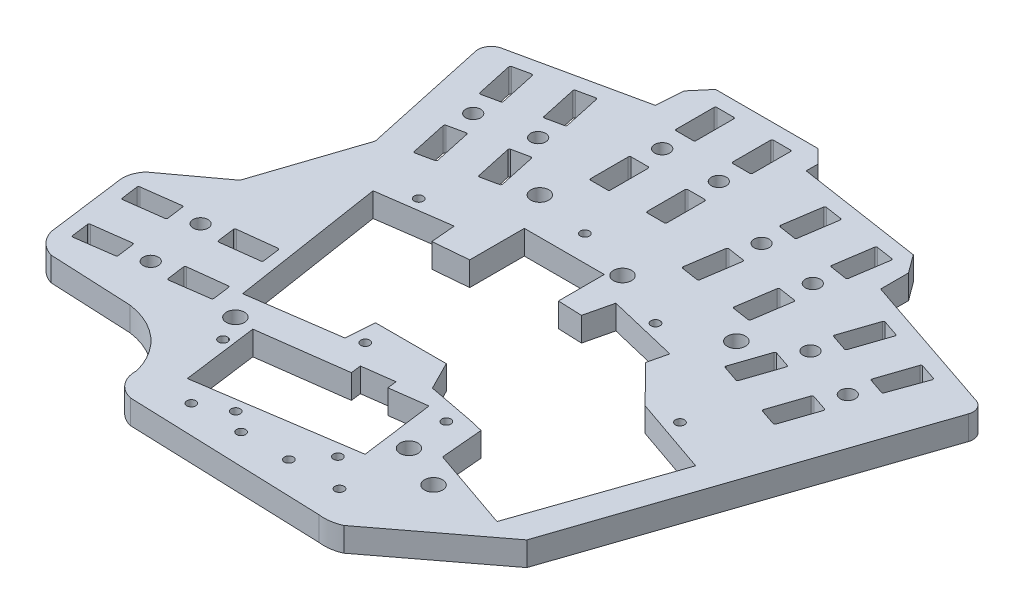
SolidWorks part; units mm, degrees
ref_plane "Front Plane" through (0, 0, 0) normal (0, 0, 1) x (1, 0, 0)
ref_plane "Top Plane" through (0, 0, 0) normal (0, 1, 0) x (1, 0, 0)
ref_plane "Right Plane" through (0, 0, 0) normal (1, 0, 0) x (0, 0, -1)
sketch "Sketch1" plane through (0, 0, 0) normal (0, 1, 0) x (1, 0, 0)
  line L0 (414.8299, -62.9754) -> (414.8299, 577.0246) construction
  line L1 (0, -2.5947) -> (-1.673, 9.9781)
  line L128 (-0.4306, 75.7337) -> (-0.1016, 80.2321)
  line L129 (44.8017, 72.6509) -> (44.8017, 68.0109)
  line L130 (-18.2349, 69.3257) -> (-15.0094, 70.0232)
  line L131 (-13.7962, 48.8002) -> (-15.2229, 55.3977)
  line L132 (17.4784, 66.3016) -> (14.1784, 66.3016)
  line L136 (-8.0429, 64.6237) -> (-4.8175, 65.3212)
  line L137 (37.2899, 67.114) -> (40.5526, 66.6193)
  line L138 (47.537, 57.3204) -> (49.7003, 63.7144)
  line L139 (50.663, 56.2628) -> (47.537, 57.3204)
  line L140 (-15.9879, 9.9957) -> (-16.4404, 13.4126)
  line L141 (-30.1274, 8.2215) -> (-30.567, 11.5414)
  line L142 (12.5856, 13.6137) -> (17.8315, 14.3117)
  line L145 (-0.1016, 80.2321) -> (2.2923, 83.0516)
  line L146 (-13.5827, 63.4257) -> (-16.8082, 62.7282)
  line L147 (-6.2442, 71.9187) -> (-9.4696, 71.2212)
  line L148 (49.7003, 63.7144) -> (52.8262, 62.6568)
  line L149 (-17.2671, 19.6546) -> (-10.5698, 20.4923)
  line L150 (24.079, 13.5635) -> (25.7132, 1.2828)
  line L152 (-9.4696, 71.2212) -> (-8.0429, 64.6237)
  line L153 (14.1784, 80.5516) -> (14.1784, 73.8016)
  line L154 (28.2605, 75.3105) -> (31.5232, 74.8157)
  line L155 (-10.5698, 20.4923) -> (-11.003, 23.7637)
  line L158 (-29.1205, 3.861) -> (-15.3607, 3.2228)
  line L159 (4.748, 80.5516) -> (8.048, 80.5516)
  line L160 (25.1119, 54.5479) -> (26.1239, 61.2216)
  line L161 (-17.7067, 22.9746) -> (-17.2671, 19.6546)
  line L162 (17.8315, 14.3117) -> (18.038, 12.7597)
  line L164 (-4.9467, 50.7139) -> (-1.7212, 51.4114)
  line L165 (31.5232, 74.8157) -> (30.5111, 68.142)
  line L166 (36.1654, 59.6988) -> (35.1534, 53.0251)
  line L167 (-24.7018, 18.6674) -> (-25.1351, 21.9389)
  line L169 (42.5794, 75.6677) -> (44.8017, 72.6509)
  line L170 (8.048, 66.3016) -> (8.048, 59.5516)
  line L171 (29.3866, 60.7268) -> (28.3746, 54.0531)
  line L172 (-23.8755, 12.4276) -> (-23.4422, 9.1562)
  line L173 (-9.7367, 14.2018) -> (-9.3035, 10.9303)
  line L175 (44.8017, 68.0109) -> (66.3992, 60.704)
  line L176 (-10.5708, 49.4977) -> (-13.7962, 48.8002)
  line L177 (4.748, 73.8016) -> (4.748, 80.5516)
  line L178 (38.4161, 52.5303) -> (39.4281, 59.204)
  line L179 (42.9702, 43.822) -> (45.1334, 50.216)
  line L180 (-31.8266, 21.0527) -> (-31.3934, 17.7812)
  line L181 (12.8129, 11.9057) -> (12.5856, 13.6137)
  line L182 (25.7132, 1.2828) -> (0, -2.5947)
  line L183 (-21.396, 71.1999) -> (-0.4306, 75.7337)
  line L184 (-16.8082, 62.7282) -> (-18.2349, 69.3257)
  line L185 (17.4784, 80.5516) -> (14.1784, 80.5516)
  line L186 (17.4784, 59.5516) -> (17.4784, 66.3016)
  line L187 (56.9812, 54.1252) -> (59.9745, 53.1125)
  line L188 (48.2594, 49.1584) -> (46.0962, 42.7644)
  line L189 (57.6372, 45.9857) -> (54.5113, 47.0433)
  line L190 (-16.4404, 13.4126) -> (-9.7367, 14.2018)
  line L192 (27.2484, 68.6368) -> (28.2605, 75.3105)
  line L193 (52.8262, 62.6568) -> (50.663, 56.2628)
  line L194 (59.1439, 60.5178) -> (56.9812, 54.1252)
  line L195 (52.3481, 40.6493) -> (55.474, 39.5917)
  line L196 (-23.4422, 9.1562) -> (-30.1274, 8.2215)
  line L197 (-1.673, 9.9781) -> (12.8129, 11.9057)
  line L200 (-15.0094, 70.0232) -> (-13.5827, 63.4257)
  line L201 (8.048, 73.8016) -> (4.748, 73.8016)
  line L202 (14.1784, 59.5516) -> (17.4784, 59.5516)
  line L203 (39.4281, 59.204) -> (36.1654, 59.6988)
  line L204 (46.0962, 42.7644) -> (42.9702, 43.822)
  line L208 (2.2923, 83.0516) -> (19.2923, 83.0516)
  line L209 (21.5696, 78.8537) -> (42.5794, 75.6677)
  line L210 (-24.2083, 30.3699) -> (-33.1809, 23.7603)
  line L211 (-15.2229, 55.3977) -> (-11.9975, 56.0952)
  line L212 (-6.3734, 57.3114) -> (-4.9467, 50.7139)
  line L213 (14.1784, 66.3016) -> (14.1784, 59.5516)
  line L214 (54.5113, 47.0433) -> (52.3481, 40.6493)
  line L217 (-18.5836, 47.2829) -> (-23.2066, 68.6607)
  line L218 (19.2923, 83.0516) -> (21.5696, 80.8227)
  line L219 (-34.2129, 20.029) -> (-32.5222, 7.2627)
  line L220 (-4.8175, 65.3212) -> (-6.2442, 71.9187)
  line L221 (-3.1479, 58.0089) -> (-6.3734, 57.3114)
  line L222 (4.748, 66.3016) -> (8.048, 66.3016)
  line L223 (40.5526, 66.6193) -> (41.5647, 73.293)
  line L224 (41.5647, 73.293) -> (38.302, 73.7877)
  line L226 (-24.2083, 30.3699) -> (-18.5836, 47.2829)
  line L227 (14.1784, 73.8016) -> (17.4784, 73.8016)
  line L228 (30.5111, 68.142) -> (27.2484, 68.6368)
  line L229 (38.302, 73.7877) -> (37.2899, 67.114)
  line L230 (-25.1351, 21.9389) -> (-31.8266, 21.0527)
  line L231 (-11.003, 23.7637) -> (-17.7067, 22.9746)
  line L233 (21.5696, 80.8227) -> (21.5696, 78.8537)
  line L234 (-1.9091, -10.1276) -> (30.562, -11.2693)
  line L235 (17.4784, 73.8016) -> (17.4784, 80.5516)
  line L236 (4.748, 59.5516) -> (4.748, 66.3016)
  line L237 (26.1239, 61.2216) -> (29.3866, 60.7268)
  line L239 (-9.3035, 10.9303) -> (-15.9879, 9.9957)
  line L241 (-11.9975, 56.0952) -> (-10.5708, 49.4977)
  line L242 (35.1534, 53.0251) -> (38.4161, 52.5303)
  line L243 (62.2699, 59.4603) -> (59.1439, 60.5178)
  line L244 (-31.3934, 17.7812) -> (-24.7018, 18.6674)
  line L245 (-30.567, 11.5414) -> (-23.8755, 12.4276)
  line L246 (18.038, 12.7597) -> (24.079, 13.5635)
  line L247 (-1.7212, 51.4114) -> (-3.1479, 58.0089)
  line L248 (8.048, 80.5516) -> (8.048, 73.8016)
  line L249 (8.048, 59.5516) -> (4.748, 59.5516)
  line L250 (28.3746, 54.0531) -> (25.1119, 54.5479)
  line L251 (45.1334, 50.216) -> (48.2594, 49.1584)
  line L252 (55.474, 39.5917) -> (57.6372, 45.9857)
  line L254 (-13.6102, 55.7464) -> (-15.1954, 63.077) construction
  line L256 (59.9745, 53.1125) -> (62.2699, 59.4603)
  line L257 (-4.7607, 57.6601) -> (-6.4302, 64.9725) construction
  line L258 (6.398, 66.3016) -> (6.398, 73.8016) construction
  line L259 (15.8284, 66.3016) -> (15.8284, 73.8016) construction
  line L260 (46.6964, 49.6872) -> (47.069, 50.7886) construction
  line L261 (56.0742, 46.5145) -> (58.4778, 53.6189) construction
  line L262 (-24.9184, 20.3032) -> (-17.4869, 21.3146) construction
  line L263 (-16.2142, 11.7042) -> (-23.6588, 10.7919) construction
  line L264 (27.7553, 60.9742) -> (28.8798, 68.3894) construction
  line L265 (37.7968, 59.4514) -> (38.9213, 66.8666) construction
  line L272 (66.3992, 60.704) -> (68.8544, 59.8733)
  line L273 (70.108, 57.3378) -> (51.5211, 2.3994)
  line L274 (51.5211, 2.3994) -> (34.2012, -10.7501)
  line L299 (47.4976, 52.0553) -> (49.1, 56.7916) construction
  line L302 (19.7057, 47.104) -> (19.7057, 42.0865)
  line L309 (7.2943, 16.3661) -> (7.6276, 21.104)
  line L310 (7.6276, 21.104) -> (19.4078, 21.104)
  line L317 (-10.9036, 40.0286) -> (4.9406, 42.2472) construction
  line L319 (0.2418, 41.5893) -> (0.598, 37.5071)
  line L320 (0.598, 37.5071) -> (6.398, 38.0133)
  line L321 (6.398, 38.0133) -> (6.398, 47.104)
  line L322 (6.398, 47.104) -> (19.7057, 47.104)
  line L323 (19.7057, 42.0865) -> (19.7057, 39.4743)
  line L324 (24.8019, 43.9355) -> (23.6987, 39.3179)
  line L325 (23.6987, 39.3179) -> (19.7057, 39.4743)
  line L326 (24.8019, 43.9355) -> (36.6086, 41.1145)
  line L327 (25.1826, 43.2788) -> (36.6086, 41.1145) construction
  line L328 (36.6086, 41.1145) -> (35.941, 37.5897) construction
  line L329 (36.6086, 41.1145) -> (35.8276, 37.8454)
  line L330 (35.8276, 37.8454) -> (42.0285, 31.5818)
  line L332 (32.5456, 7.3504) -> (46.3891, 2.5621)
  line L333 (46.3891, 2.5621) -> (54.8882, 27.1338)
  line L335 (42.0285, 31.5818) -> (54.8882, 27.1338)
  line L337 (19.4078, 21.104) -> (21.7804, 16.4205)
  line L338 (21.7804, 16.4205) -> (29.6863, 14.9001)
  line L339 (29.6863, 14.9001) -> (31.9336, 14.3632)
  line L340 (-11.6079, 39.93) -> (-7.6294, 14.2361)
  line L341 (-7.6294, 14.2361) -> (7.2943, 16.3661)
  line L342 (-11.6079, 39.93) -> (0.2418, 41.5893)
  line L345 (31.9336, 14.3632) -> (32.5456, 7.3504)
  arc A39 (-33.1809, 23.7603) -> (-34.2129, 20.029) centre (-30.0537, 20.8871) ccw
  circle A40 centre (-5.5285, 61.3308) radius 1.25
  circle A41 centre (15.8284, 70.0516) radius 1.25
  circle A43 centre (-14.4198, 59.408) radius 1.25
  circle A44 centre (12.1847, 51.3928) radius 0.75
  arc A45 (-15.3607, 3.2228) -> (-5.337, -5.6661) centre (-16.9425, -8.657) cw
  circle A46 centre (47.8982, 53.2394) radius 1.25
  circle A48 centre (-4.8264, 10.2313) radius 1.5
  circle A49 centre (-2.6471, 5.9989) radius 0.75
  circle A50 centre (3.9045, -5.8292) radius 0.75
  circle A51 centre (23.7898, -1.3252) radius 0.75
  arc A53 (34.2012, -10.7501) -> (30.562, -11.2693) centre (31.4838, -4.7168) cw
  circle A54 centre (28.3175, 64.6818) radius 1.25
  circle A55 centre (40.317, 48.4759) radius 1.5
  circle A57 centre (20.131, -5.8292) radius 0.75
  circle A59 centre (-21.2027, 20.8089) radius 1.25
  arc A61 (-32.5222, 7.2627) -> (-29.1205, 3.861) centre (-27.7256, 8.6576) ccw
  circle A62 centre (6.398, 70.0516) radius 1.25
  circle A63 centre (-19.9365, 11.248) radius 1.25
  arc A64 (-5.337, -5.6661) -> (-1.9091, -10.1276) centre (-1.006, -5.886) ccw
  circle A65 centre (38.359, 63.159) radius 1.25
  circle A66 centre (8.761, -3.2983) radius 0.75
  circle A67 centre (28.5591, -5.8292) radius 0.75
  circle A69 centre (2.8796, 53.2042) radius 1.5
  circle A70 centre (21.3669, 48.4759) radius 1.5
  circle A71 centre (28.4975, 5.8033) radius 1.5
  arc A72 (-23.2066, 68.6607) -> (-21.396, 71.1999) centre (-21.0316, 69.025) cw
  circle A73 centre (57.276, 50.0667) radius 1.25
  circle A74 centre (12.1847, -5.8292) radius 0.75
  arc A77 (70.108, 57.3378) -> (68.8544, 59.8733) centre (68.2134, 57.9788) ccw
  circle A79 centre (30.9955, 44.343) radius 0.75
  circle A80 centre (47.3149, 32.0935) radius 0.75
  circle A81 centre (-6.6778, 42.6019) radius 0.75
  circle A83 centre (9.6505, 17.369) radius 0.7627
  circle A84 centre (35.8276, 2.5621) radius 1.5
  circle A85 centre (27.7553, 12.7597) radius 0.75
  point P28 (-5.7897, 41.1181)
  point P29 (12.1847, 50.6428)
  point P30 (31.1361, 45.7394)
  point P31 (47.2602, 34.058)
  point P32 (-3.3264, 10.2313)
  point P38 (14.3264, -10.6984)
  dimension "D18" = 2.5
  dimension "D19" = 2.5
  dimension "D28" = 2.5
  dimension "D29" = 2.5
  dimension "D41" = 2.5
  dimension "D42" = 2.5
  dimension "D53" = 2.5
  dimension "D54" = 2.5
  dimension "D64" = 2.5
  dimension "D65" = 2.5
  dimension "D35" = 3
  dimension "D62" = 3
  dimension "D63" = 3
  dimension "D67" = 3
  dimension "D75" = 3
  dimension "D76" = 1.5254
  dimension "D77" = 1.5
  dimension "D78" = 1.5
  dimension "D79" = 1.5
  dimension "D80" = 1.5
  dimension "D81" = 1.5
  dimension "D82" = 1.5
  dimension "D83" = 1.5
  dimension "D84" = 1.5
  dimension "D85" = 1.5
  dimension "D86" = 1.5
  dimension "D87" = 26
  dimension "D88" = 26
  dimension "D89" = 1.5
  dimension "D94" = 2
  dimension "D34" = 1.5
  dimension "D92" = 3
  dimension "D100" = 26
  dimension "D1" = 2.5
  dimension "D2" = 17
  dimension "D4" = 22.8
  dimension "D5" = 21.25
  dimension "D6" = 2.5
  dimension "D7" = 2.5
  dimension "D8" = 2.5
  dimension "D9" = 2.5
  dimension "D10" = 2.5
  dimension "D11" = 2.5
  dimension "D12" = 21.45
  dimension "D13" = 3.3
  dimension "D14" = 3.3
  dimension "D15" = 2.5
  dimension "D16" = 3.3
  dimension "D17" = 3.3
  dimension "D20" = 3.3
  dimension "D21" = 3.3
  dimension "D22" = 3.3
  dimension "D23" = 6.75
  dimension "D24" = 3.3
  dimension "D25" = 6.75
  dimension "D26" = 6.75
  dimension "D27" = 6.75
  dimension "D30" = 6.75
  dimension "D31" = 6.75
  dimension "D32" = 6.75
  dimension "D33" = 6.75
  dimension "D36" = 7.5
  dimension "D37" = 3.3
  dimension "D38" = 3.3
  dimension "D39" = 6.75
  dimension "D40" = 6.75
  dimension "D43" = 7.5
  dimension "D44" = 6.75
  dimension "D45" = 6.75
  dimension "D46" = 6.75
  dimension "D47" = 6.75
  dimension "D48" = 6.75
  dimension "D49" = 3.3
  dimension "D50" = 3.3
  dimension "D51" = 3.3
  dimension "D52" = 3.3
  dimension "D55" = 7.5
  dimension "D56" = 6.75
  dimension "D57" = 6.75
  dimension "D58" = 6.75
  dimension "D59" = 6.75
  dimension "D60" = 3.75
  dimension "D61" = 3.75
  dimension "D66" = 3.75
  dimension "D68" = 3.75
  dimension "D69" = 3.75
  dimension "D70" = 3.75
  dimension "D71" = 3.75
  dimension "D72" = 3.75
  dimension "D73" = 3.75
  dimension "D74" = 7.5
  dimension "D90" = 4.5
  dimension "D91" = 5.8
  dimension "D93" = 93.75
  dimension "D95" = 26
  dimension "D96" = 6.67
  dimension "D97" = 3.3
  dimension "D98" = 3.3
  dimension "D99" = 3.3
extrude "Boss-Extrude1" add sketch "Sketch1" along normal blind 4
fillet "Fillet2" radius 0.25 80 edges at (-23.4422, 2, -9.1562) (-9.3035, 2, -10.9303) (-10.5698, 2, -20.4923) (-24.7018, 2, -18.6674) (-9.7367, 2, -14.2018) (-23.8755, 2, -12.4276) (-11.003, 2, -23.7637) (-25.1351, 2, -21.9389) (-17.7067, 2, -22.9746) (-16.4404, 2, -13.4126) (-30.567, 2, -11.5414) (-31.8266, 2, -21.0527) (-17.2671, 2, -19.6546) (-15.9879, 2, -9.9957) (-30.1274, 2, -8.2215) (-31.3934, 2, -17.7812) (55.474, 2, -39.5917) (52.3481, 2, -40.6493) (57.6372, 2, -45.9857) (54.5113, 2, -47.0433) (46.0962, 2, -42.7644) (42.9702, 2, -43.822) (48.2594, 2, -49.1584) (45.1334, 2, -50.216) (62.2699, 2, -59.4603) (59.9745, 2, -53.1125) (59.1439, 2, -60.5178) (56.9812, 2, -54.1252) (52.8262, 2, -62.6568) (50.663, 2, -56.2628) (47.537, 2, -57.3204) (49.7003, 2, -63.7144) (38.302, 2, -73.7877) (36.1654, 2, -59.6988) (40.5526, 2, -66.6193) (38.4161, 2, -52.5303) (28.3746, 2, -54.0531) (26.1239, 2, -61.2216) (29.3866, 2, -60.7268) (39.4281, 2, -59.204) (41.5647, 2, -73.293) (37.2899, 2, -67.114) (35.1534, 2, -53.0251) (25.1119, 2, -54.5479) (27.2484, 2, -68.6368) (31.5232, 2, -74.8157) (30.5111, 2, -68.142) (28.2605, 2, -75.3105) (17.4784, 2, -59.5516) (14.1784, 2, -59.5516) (17.4784, 2, -66.3016) (14.1784, 2, -66.3016) (8.048, 2, -59.5516) (4.748, 2, -59.5516) (8.048, 2, -66.3016) (4.748, 2, -66.3016) (17.4784, 2, -73.8016) (14.1784, 2, -73.8016) (8.048, 2, -73.8016) (4.748, 2, -73.8016) (14.1784, 2, -80.5516) (17.4784, 2, -80.5516) (8.048, 2, -80.5516) (4.748, 2, -80.5516) (-1.7212, 2, -51.4114) (-4.9467, 2, -50.7139) (-3.1479, 2, -58.0089) (-6.3734, 2, -57.3114) (-10.5708, 2, -49.4977) (-13.7962, 2, -48.8002) (-11.9975, 2, -56.0952) (-15.2229, 2, -55.3977) (-4.8175, 2, -65.3212) (-8.0429, 2, -64.6237) (-13.5827, 2, -63.4257) (-16.8082, 2, -62.7282) (-6.2442, 2, -71.9187) (-9.4696, 2, -71.2212) (-15.0094, 2, -70.0232) (-18.2349, 2, -69.3257)
